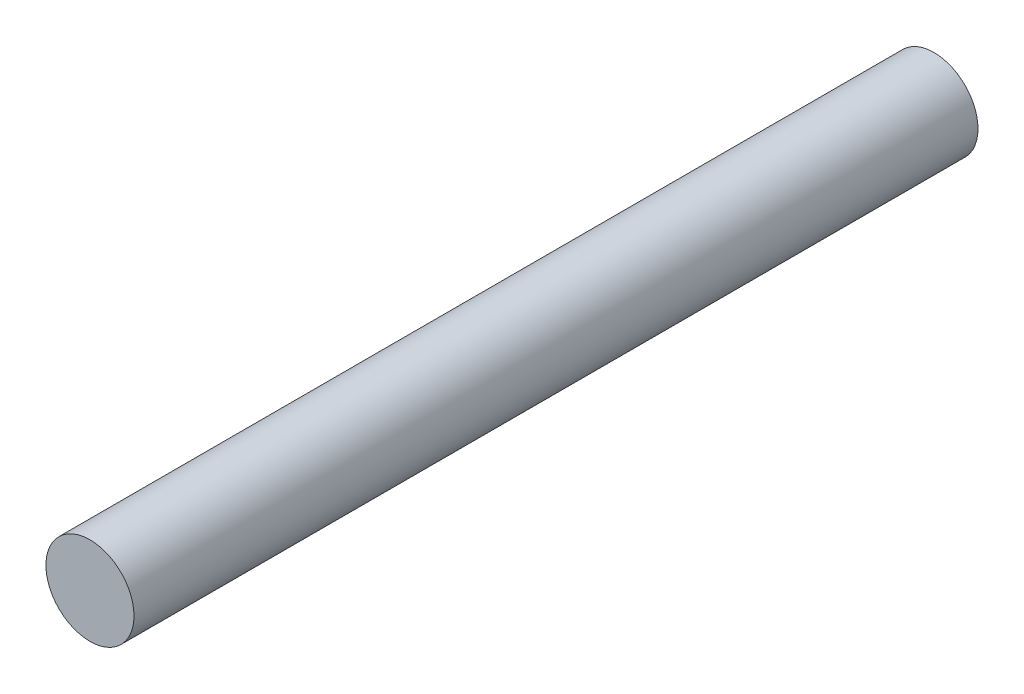
SolidWorks part; units mm, degrees
ref_plane "前基準面" through (0, 0, 0) normal (0, 0, 1) x (1, 0, 0)
ref_plane "上基準面" through (0, 0, 0) normal (0, 1, 0) x (1, 0, 0)
ref_plane "右基準面" through (0, 0, 0) normal (1, 0, 0) x (0, 0, -1)
sketch "草圖1" plane through (0, 0, 0) normal (0, 0, 1) x (1, 0, 0)
  circle A0 centre (0, 0) radius 6
  dimension "D1" = 12
extrude "填料-伸長1" add sketch "草圖1" along normal blind 115
